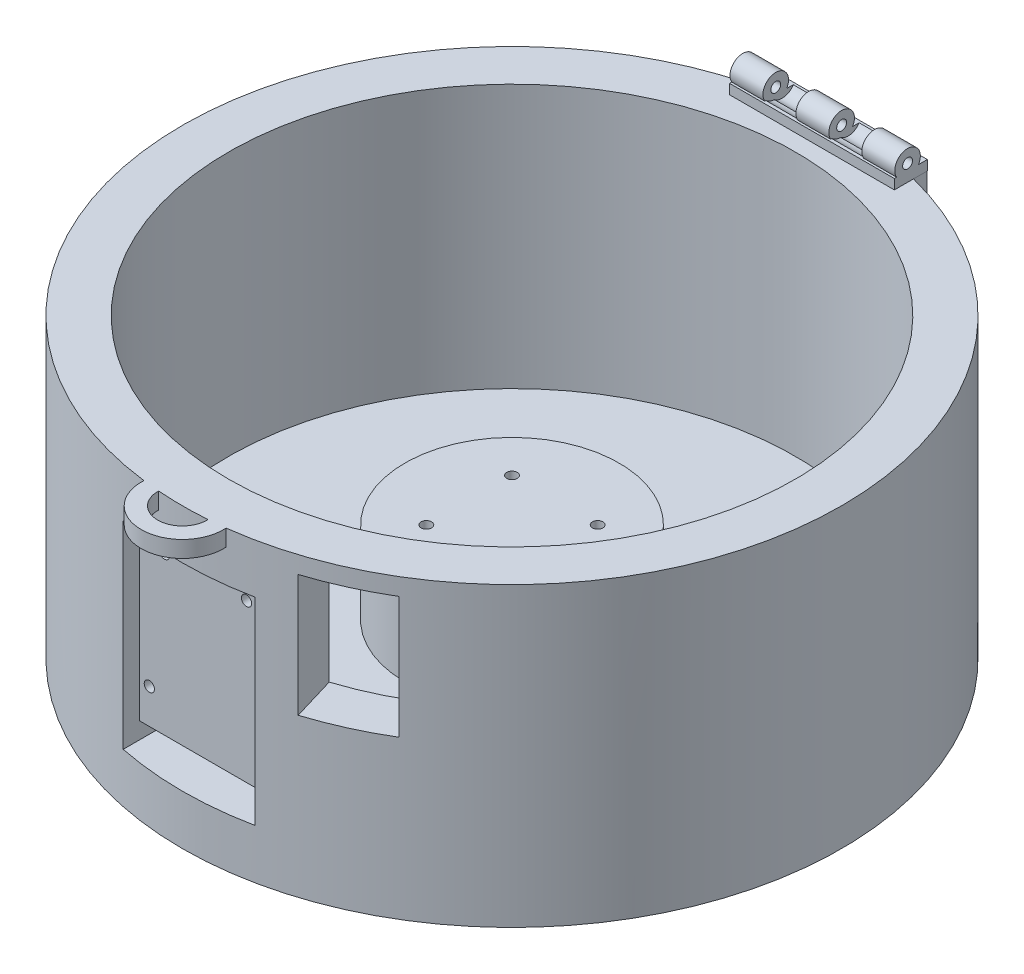
SolidWorks part; units mm, degrees
material "ABS"
ref_plane "Front Plane" through (0, 0, 0) normal (0, 0, 1) x (1, 0, 0)
ref_plane "Top Plane" through (0, 0, 0) normal (0, 1, 0) x (1, 0, 0)
ref_plane "Right Plane" through (0, 0, 0) normal (1, 0, 0) x (0, 0, -1)
sketch "Sketch1" plane through (0, 0, 0) normal (0, 1, 0) x (1, 0, 0)
  circle A1 centre (0, 0) radius 100
extrude "Boss-Extrude3" add sketch "Sketch1" along normal blind 90
ref_plane "Plane1" through (0, 0, 105) normal (0, 0, 1) x (1, 0, 0)
sketch "Sketch4" plane through (0, 0, 105) normal (0, 0, 1) x (1, 0, 0)
  line L26 (-20, 75) -> (20, 75)
  line L27 (-20, 75) -> (-20, 15)
  line L28 (-20, 15) -> (20, 15)
  line L29 (20, 75) -> (20, 15)
  line L30 (-20, 75) -> (20, 15) construction
  line L31 (-20, 15) -> (20, 75) construction
  point P5 (0, 45)
  dimension "D1" = 60
  dimension "D2" = 40
  dimension "D3" = 45
extrude "Cut-Extrude2" cut sketch "Sketch4" along normal blind 26 and the other way blind 12
sketch "Sketch12" plane through (0, 0, 0) normal (0, -1, 0) x (1, 0, 0)
  circle A1 centre (0, 0) radius 100
  circle A2 centre (0, 0) radius 100
  dimension "D1" = 0
extrude "Boss-Extrude4" add sketch "Sketch12" along normal blind 0.1
sketch "Sketch13" plane through (0, 90, 0) normal (0, 1, 0) x (1, 0, 0)
  circle A0 centre (0, 0) radius 86
extrude "Cut-Extrude8" cut sketch "Sketch13" against normal blind 80 contours A0
sketch "Sketch18" plane through (0, 10, 0) normal (0, 1, 0) x (1, 0, 0)
  circle A0 centre (0, 0) radius 32.5
  dimension "D1" = 65
extrude "Boss-Extrude5" add sketch "Sketch18" along normal blind 25
sketch "Sketch16" plane through (0, -0.1, 0) normal (0, -1, 0) x (1, 0, 0)
  line L0 (0, 0) -> (-8.9936, 0) construction
  line L1 (0, 0) -> (0, 9.8047) construction
  circle A2 centre (-13, 13) radius 1.6
  circle A5 centre (13, 13) radius 1.6
  circle A6 centre (13, -13) radius 1.6
  circle A7 centre (-13, -13) radius 1.6
  dimension "D3" = 3.2
  dimension "D1" = 13
  dimension "D2" = 13
extrude "Cut-Extrude11" cut sketch "Sketch16" against normal through all
sketch "Sketch17" plane through (0, -0.1, 0) normal (0, -1, 0) x (1, 0, 0)
  circle A0 centre (-13, 13) radius 3
  circle A1 centre (13, 13) radius 3
  circle A2 centre (-13, -13) radius 3
  circle A3 centre (13, -13) radius 3
  dimension "D1" = 6
  dimension "D2" = 6
  dimension "D3" = 6
  dimension "D4" = 6
extrude "Cut-Extrude12" cut sketch "Sketch17" against normal blind 30
sketch "Sketch19" plane through (0, -0.1, 0) normal (0, -1, 0) x (1, 0, 0)
  circle A0 centre (0, 0) radius 30
  dimension "D1" = 60
extrude "Cut-Extrude13" cut sketch "Sketch19" against normal blind 25 contours A0
sketch "Sketch20" plane through (0, 0, 93) normal (0, 0, 1) x (1, 0, 0)
  line L0 (20, 75) -> (20, 15) construction
  line L1 (-20, 15) -> (20, 15)
  line L2 (-20, 15) -> (-20, 20)
  line L3 (-20, 20) -> (20, 20)
  line L4 (20, 15) -> (20, 20)
  dimension "D1" = 5
extrude "Cut-Extrude14" cut sketch "Sketch20" against normal blind 25
sketch "Sketch21" plane through (0, 0, 93) normal (0, 0, 1) x (1, 0, 0)
  line L0 (20, 75) -> (-20, 75) construction
  circle A0 centre (12.45, 67.8) radius 1.55
  circle A1 centre (-12.45, 67.8) radius 1.55
  circle A2 centre (-17.05, 30.54) radius 1.55
  circle A3 centre (17.05, 30.54) radius 1.55
  dimension "D3" = 3.1
  dimension "D4" = 3.1
  dimension "D9" = 3.1
  dimension "D10" = 3.1
  dimension "D1" = 12.45
  dimension "D2" = 24.9
  dimension "D5" = 7.2
  dimension "D6" = 7.2
  dimension "D7" = 17.05
  dimension "D8" = 17.05
  dimension "D11" = 37.26
  dimension "D12" = 37.26
extrude "Cut-Extrude15" cut sketch "Sketch21" against normal blind 25
ref_plane "Plane2" through (22.2041, 47.7941, -296.4042) normal (0, 1, 0) x (1, 0, 0)
sketch "Sketch23" plane through (0, 90, 0) normal (0, 1, 0) x (1, 0, 0)
  line L0 (0, 0) -> (0, 93.5235)
  line L2 (-25, 86.0235) -> (25, 86.0235)
  line L3 (-25, 86.0235) -> (-25, 101.0235)
  line L4 (-25, 101.0235) -> (25, 101.0235)
  line L5 (25, 86.0235) -> (25, 101.0235)
  line L6 (-25, 86.0235) -> (25, 101.0235) construction
  line L7 (-25, 101.0235) -> (25, 86.0235) construction
  dimension "D1" = 15
  dimension "D2" = 50
extrude "Boss-Extrude6" add sketch "Sketch23" along normal blind 3 contours L3 L2 L5 L4
sketch "Sketch24" plane through (0, 93, 0) normal (0, 1, 0) x (1, 0, 0)
  line L0 (0, 86.0235) -> (0, 92.0235)
  line L1 (-25, 86.0235) -> (25, 86.0235) construction
  line L3 (-25, 92.0235) -> (25, 92.0235)
  line L4 (-25, 98.0235) -> (25, 98.0235)
  line L5 (-25, 92.0235) -> (-25, 98.0235)
  line L6 (25, 92.0235) -> (25, 98.0235)
  dimension "D1" = 6
extrude "Boss-Extrude7" add sketch "Sketch24" along normal blind 4 contours L6 L4 L5 L3
sketch "Sketch25" plane through (25, 0, 0) normal (1, 0, 0) x (0, 0, -1)
  line L0 (92.0235, 97) -> (98.0235, 93)
  circle A0 centre (95.0235, 95) radius 1.5
  dimension "D1" = 3
extrude "Cut-Extrude17" cut sketch "Sketch25" against normal through all contours A0
sketch "Sketch27" plane through (25, 0, 0) normal (1, 0, 0) x (0, 0, -1)
  line L1 (92.0235, 97) -> (98.0235, 97) construction
  line L2 (92.0235, 97) -> (98.0235, 97)
  arc A0 (92.0235, 97) -> (98.0235, 97) centre (95.0235, 95.5) cw
extrude "Boss-Extrude8" add sketch "Sketch27" against normal blind 50 contours L2 A0
sketch "Sketch29" plane through (0, 0, -92.0235) normal (0, 0, 1) x (1, 0, 0)
  line L0 (-25, 93) -> (-15, 93) construction
  line L1 (-25, 93) -> (25, 93) construction
  line L2 (-15, 93) -> (-15, 104)
  line L3 (-15, 104) -> (-5, 104)
  line L4 (-5, 104) -> (-5, 93)
  line L5 (-5, 93) -> (-15, 93)
  line L6 (-5, 93) -> (5, 93) construction
  line L7 (5, 93) -> (5, 104)
  line L8 (5, 104) -> (15, 104)
  line L9 (15, 104) -> (15, 93)
  line L10 (15, 93) -> (5, 93)
  dimension "D1" = 10
  dimension "D2" = 10
  dimension "D3" = 10
  dimension "D4" = 11
  dimension "D5" = 10
extrude "Cut-Extrude20" cut sketch "Sketch29" against normal through all
sketch "Sketch30" plane through (25, 0, 0) normal (1, 0, 0) x (0, 0, -1)
  line L1 (92.0235, 93) -> (98.0235, 93)
  circle A1 centre (95.0235, 95) radius 1.5 construction
  arc A2 (92.0235, 93) -> (98.0235, 93) centre (95.0235, 96.5) ccw
extrude "Cut-Extrude21" cut sketch "Sketch30" against normal blind 10 from offset 10 contours L1 A2 offset against normal yes
pattern_linear "LPattern1" count 2 spacing 20 along (-1, 0, 0) of "Cut-Extrude21"
sketch "Sketch31" plane through (25, 0, 0) normal (1, 0, 0) x (0, 0, -1)
  circle A0 centre (95.0235, 95) radius 3.8812
  circle A1 centre (95.0235, 95) radius 1.5
extrude "Boss-Extrude9" add sketch "Sketch31" against normal blind 10
sketch "Sketch33" plane through (5, 0, 0) normal (1, 0, 0) x (0, 0, -1)
  circle A0 centre (95.0235, 95) radius 3.8812
  circle A1 centre (95.0235, 95) radius 1.5
sketch "Sketch34" plane through (-15, 0, 0) normal (1, 0, 0) x (0, 0, -1)
  circle A0 centre (95.0235, 95) radius 3.8812
  circle A1 centre (95.0235, 95) radius 1.5
extrude "Boss-Extrude11" add sketch "Sketch33" against normal blind 10
extrude "Boss-Extrude12" add sketch "Sketch34" against normal blind 10
sketch "Sketch36" plane through (15, 0, 0) normal (-1, 0, 0) x (0, 0, 1)
  circle A0 centre (-97.0292, 95.0488) radius 3.8812
  circle A1 centre (-97.0292, 95.0488) radius 1.5
sketch "Sketch37" plane through (-5, 0, 0) normal (-1, 0, 0) x (0, 0, 1)
  circle A0 centre (-97.0098, 94.9871) radius 3.8812
  circle A1 centre (-97.0098, 94.9871) radius 1.5
extrude "Cut-Extrude22" cut sketch "Sketch36" along normal blind 10
extrude "Cut-Extrude23" cut sketch "Sketch37" along normal blind 10
sketch "Sketch38" plane through (0, 93, 0) normal (0, 1, 0) x (1, 0, 0)
  line L0 (25, 86.0235) -> (25, 91.6972) construction
  line L1 (-25, 86.0235) -> (25, 86.0235)
  line L2 (-25, 86.0235) -> (-25, 91.0235)
  line L3 (-25, 91.0235) -> (25, 91.0235)
  line L4 (25, 86.0235) -> (25, 91.0235)
  dimension "D1" = 5
extrude "Cut-Extrude24" cut sketch "Sketch38" against normal blind 3
sketch "Sketch39" plane through (0, 90, 0) normal (0, -1, 0) x (-1, 0, 0)
  line L1 (25, 101.0235) -> (-24.9708, 101.0235)
  line L2 (25, 101.0235) -> (25, 100.0184)
  line L3 (25, 100.0184) -> (-24.9708, 100.0184)
  line L4 (-24.9708, 101.0235) -> (-24.9708, 100.0184)
extrude "Boss-Extrude13" add sketch "Sketch39" along normal blind 10
sketch "Sketch40" plane through (0, 0, -101.0235) normal (0, 0, -1) x (-1, 0, 0)
  line L0 (25, 93) -> (25, 80) construction
  line L1 (-24.9708, 80) -> (25, 80)
  line L2 (-24.9708, 80) -> (-24.9708, 90)
  line L3 (-24.9708, 90) -> (25, 90)
  line L4 (25, 80) -> (25, 90)
extrude "Boss-Extrude14" add sketch "Sketch40" against normal up to surface (4.1914 mm away)
sketch "Sketch41" plane through (0, 90, 0) normal (0, 1, 0) x (1, 0, 0)
  circle A0 centre (0, -100) radius 12.5
  arc A1 (-25, 96.8246) -> (25, 96.8246) centre (0, 0) ccw construction
  circle A2 centre (0, -100) radius 7.5
  dimension "D1" = 25
  dimension "D2" = 15
extrude "Boss-Extrude15" add sketch "Sketch41" against normal blind 5
sketch "Sketch42" plane through (22.2041, 47.7941, -296.4042) normal (0, 1, 0) x (1, 0, 0)
  line L0 (-8.1019, -337.261) -> (12.405, -405.7625)
  line L1 (-8.1019, -337.261) -> (-1.3889, -334.1953)
  line L2 (-1.3889, -334.1953) -> (37.058, -394.3842)
  line L3 (12.405, -405.7625) -> (37.058, -394.3842)
extrude "Cut-Extrude25" cut sketch "Sketch42" along normal blind 37
